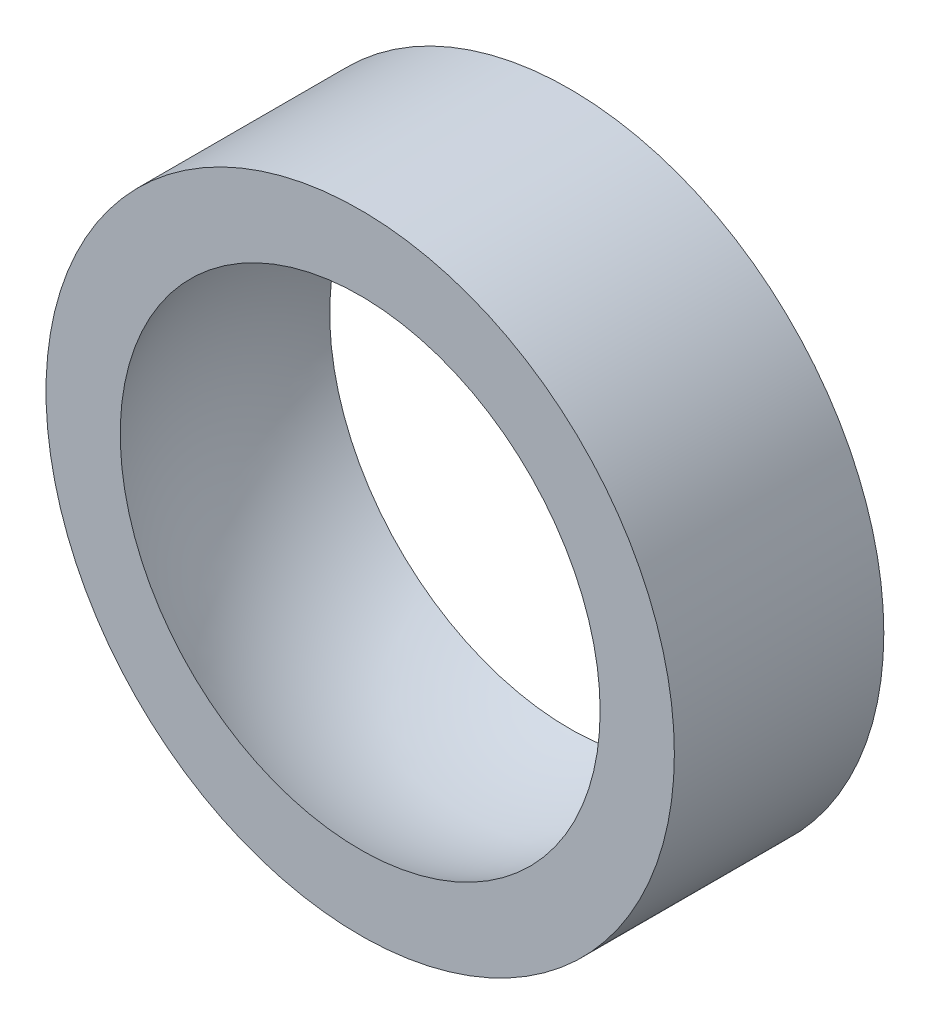
SolidWorks part; units mm, degrees
ref_plane "Plan1" through (0, 0, 0) normal (0, 0, 1) x (1, 0, 0)
ref_plane "Plan2" through (0, 0, 0) normal (0, 1, 0) x (1, 0, 0)
ref_plane "Plan3" through (0, 0, 0) normal (1, 0, 0) x (0, 0, -1)
sketch "Dia cylindre" plane through (0, 0, 0) normal (0, 0, 1) x (1, 0, 0)
  circle A0 centre (0, 0) radius 15
  dimension "Dia ext" = 30
extrude "Cylindre" add sketch "Dia cylindre" along normal mid plane 10
sketch "Esquisse sphère" plane through (0, 0, 0) normal (0, 0, 1) x (1, 0, 0)
  line L0 (0, 20) -> (0, -20) construction
  line L1 (0, 12.5) -> (0, -12.5)
  arc A0 (0, -12.5) -> (0, 12.5) centre (0, 0) ccw
  dimension "Dia" = 25
revolve "Sphère intérieure" cut sketch "Esquisse sphère" angle 360 about L0
sketch "Esquisse1" [suppressed] plane through (0, 0, 5) normal (0, 0, 1) x (1, 0, 0)
  line L1 (30, 0) -> (-30, 0)
  line L2 (30, 0) -> (30, 20)
  line L3 (30, 20) -> (-30, 20)
  line L4 (-30, 0) -> (-30, 20)
extrude "Ecorché" [suppressed] cut sketch "Esquisse1" against normal through all
